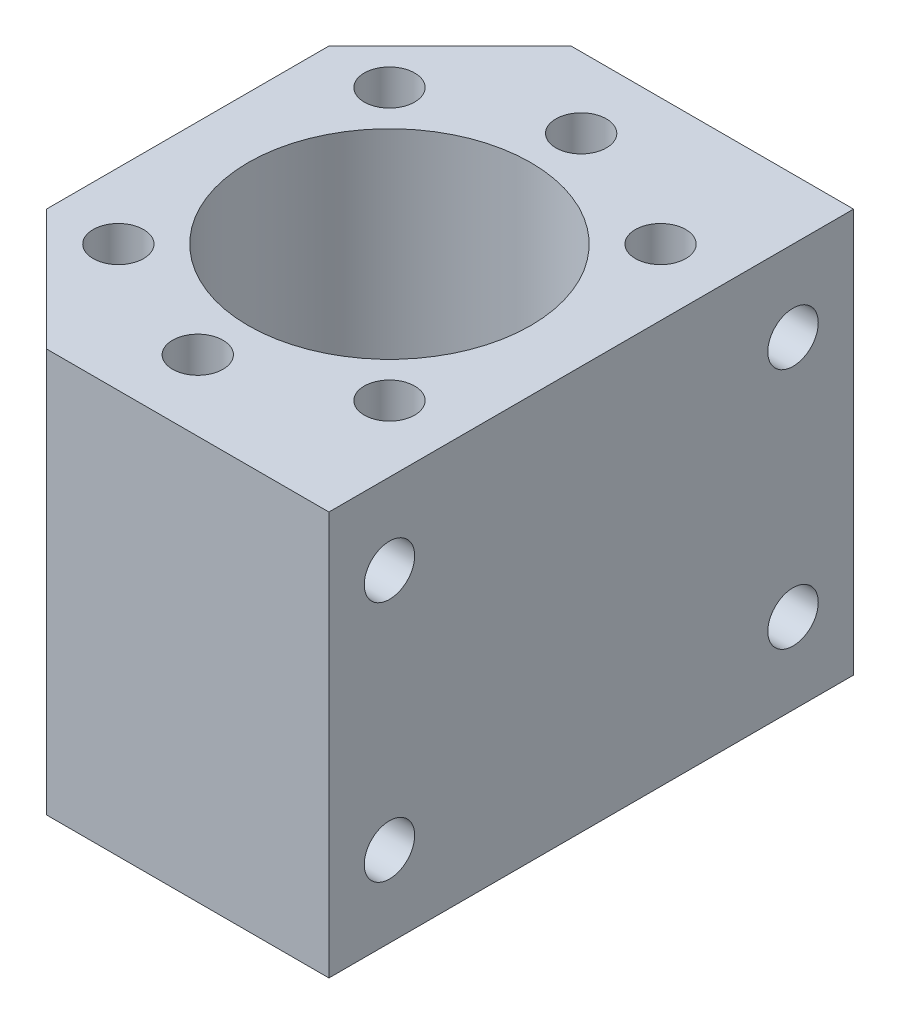
SolidWorks part; units mm, degrees
ref_plane "Спереди" through (0, 0, 0) normal (0, 0, 1) x (1, 0, 0)
ref_plane "Сверху" through (0, 0, 0) normal (0, 1, 0) x (1, 0, 0)
ref_plane "Справа" through (0, 0, 0) normal (1, 0, 0) x (0, 0, -1)
sketch "Эскиз1" plane through (0, 0, 0) normal (0, 1, 0) x (1, 0, 0)
  line L0 (-20, 14) -> (-8, 26)
  line L1 (-8, -26) -> (20, -26)
  line L2 (-20, -14) -> (-20, 14)
  line L3 (-8, 26) -> (20, 26)
  line L4 (20, -26) -> (20, 26)
  line L5 (-20, -26) -> (20, 26) construction
  line L6 (-20, 26) -> (20, -26) construction
  line L7 (-20, -14) -> (-8, -26)
  circle A0 centre (0, 0) radius 14
  point P0 (0, 0)
  dimension "D3" = 28
  dimension "D1" = 52
  dimension "D2" = 40
extrude "Бобышка-Вытянуть1" add sketch "Эскиз1" along normal blind 40
sketch "Эскиз2" plane through (0, 40, 0) normal (0, 1, 0) x (1, 0, 0)
  circle A0 centre (0, 0) radius 19 construction
  circle A1 centre (0, 19) radius 2.5
  circle A2 centre (13.435, 13.435) radius 2.5
  circle A4 centre (13.435, -13.435) radius 2.5
  circle A5 centre (0, -19) radius 2.5
  circle A6 centre (-13.435, -13.435) radius 2.5
  circle A8 centre (-13.435, 13.435) radius 2.5
  circle A9 centre (-19, 0) radius 2.5 [skipped]
  circle A10 centre (19, 0) radius 2.5 [skipped]
  point P22 (0, 0)
  dimension "D1" = 38
  dimension "D2" = 5
  dimension "D3" = 8
extrude "Вырез-Вытянуть1" cut sketch "Эскиз2" against normal blind 10
sketch "Эскиз3" plane through (20, 0, 0) normal (1, 0, 0) x (0, 0, -1)
  line L1 (-20, 8) -> (20, 8) construction
  line L2 (-20, 8) -> (-20, 32) construction
  line L3 (-20, 32) -> (20, 32) construction
  line L4 (20, 8) -> (20, 32) construction
  line L5 (-20, 8) -> (20, 32) construction
  line L6 (-20, 32) -> (20, 8) construction
  circle A0 centre (-20, 32) radius 2.5
  circle A1 centre (20, 32) radius 2.5
  circle A2 centre (20, 8) radius 2.5
  circle A3 centre (-20, 8) radius 2.5
  point P0 (0, 20)
  dimension "D3" = 5
  dimension "D4" = 5
  dimension "D5" = 5
  dimension "D6" = 5
  dimension "D1" = 24
  dimension "D2" = 40
extrude "Вырез-Вытянуть2" cut sketch "Эскиз3" against normal blind 10
